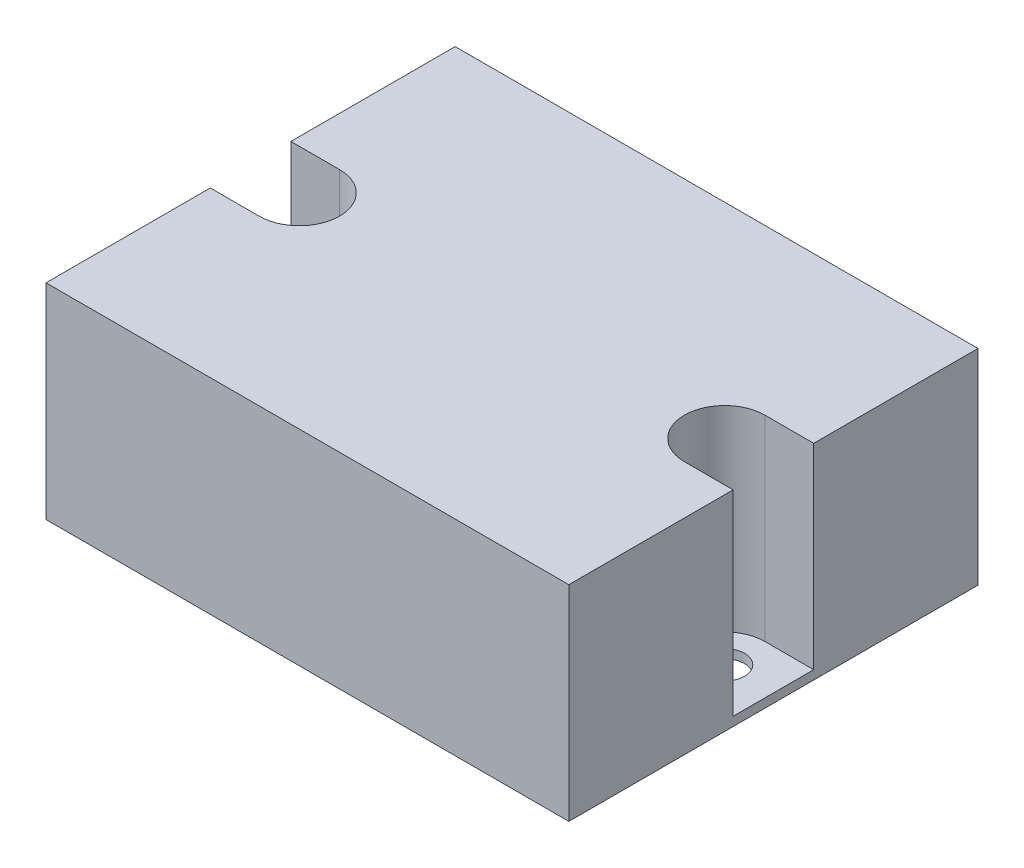
SolidWorks part; units mm, degrees
ref_plane "Front Plane" through (0, 0, 0) normal (0, 0, 1) x (1, 0, 0)
ref_plane "Top Plane" through (0, 0, 0) normal (0, 1, 0) x (1, 0, 0)
ref_plane "Right Plane" through (0, 0, 0) normal (1, 0, 0) x (0, 0, -1)
sketch "Sketch1" plane through (0, 0, 0) normal (0, 1, 0) x (1, 0, 0)
  line L0 (5.45, 25.1) -> (0, 25.1)
  line L1 (0, 0) -> (58.4, 0)
  line L2 (0, 0) -> (0, 20.6)
  line L3 (0, 45.7) -> (58.4, 45.7)
  line L4 (58.4, 0) -> (58.4, 45.7)
  line L5 (5.45, 20.6) -> (0, 20.6)
  line L6 (0, 25.1) -> (0, 45.7)
  circle A0 centre (52.95, 22.85) radius 2.225
  arc A1 (5.45, 20.6) -> (5.45, 25.1) centre (5.45, 22.85) ccw
  dimension "D7" = 4.5
  dimension "D8" = 4.45
  dimension "D1" = 58.4
  dimension "D2" = 45.7
  dimension "D3" = 0
  dimension "D4" = 0
  dimension "D5" = 47.5
  dimension "D6" = 5.45
  dimension "D9" = 22.85
  dimension "D10" = 22.85
extrude "BasePlate" add sketch "Sketch1" along normal blind 1
sketch "Sketch2" plane through (0, 1, 0) normal (0, 1, 0) x (1, 0, 0)
  line L0 (52.95, 27.35) -> (58.4, 27.35)
  line L1 (0, 45.7) -> (58.4, 45.7)
  line L2 (0, 45.7) -> (0, 27.35)
  line L3 (0, 0) -> (58.4, 0)
  line L4 (58.4, 45.7) -> (58.4, 27.35)
  line L5 (52.95, 18.35) -> (58.4, 18.35)
  line L6 (5.45, 27.35) -> (0, 27.35)
  line L7 (5.45, 18.35) -> (0, 18.35)
  line L8 (0, 18.35) -> (0, 0)
  line L9 (58.4, 18.35) -> (58.4, 0)
  arc A0 (5.45, 18.35) -> (5.45, 27.35) centre (5.45, 22.85) ccw
  arc A1 (52.95, 27.35) -> (52.95, 18.35) centre (52.95, 22.85) ccw
  dimension "D1" = 9
  dimension "D2" = 9
extrude "Boss-Extrude4" add sketch "Sketch2" along normal blind 21.9
